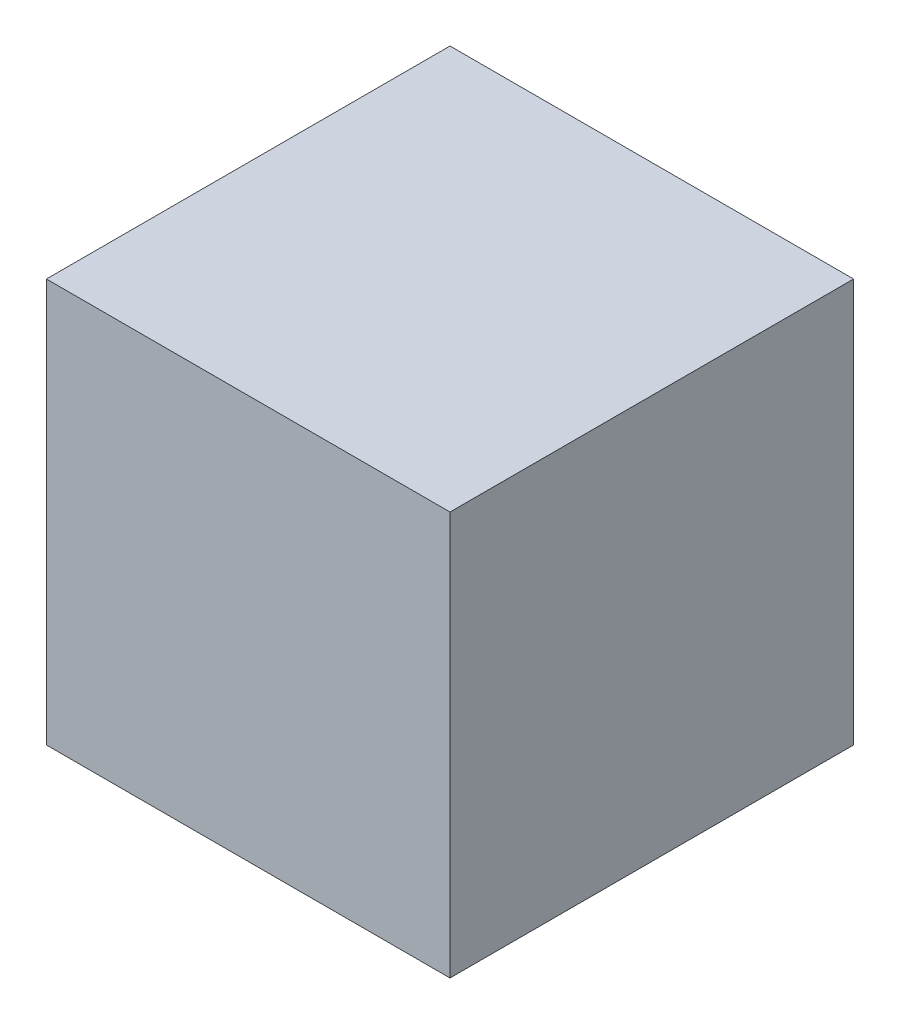
SolidWorks part; units mm, degrees
ref_plane "Ebene vorne" through (0, 0, 0) normal (0, 0, 1) x (1, 0, 0)
ref_plane "Ebene oben" through (0, 0, 0) normal (0, 1, 0) x (1, 0, 0)
ref_plane "Ebene rechts" through (0, 0, 0) normal (1, 0, 0) x (0, 0, -1)
sketch "Skizze1" plane through (0, 0, 0) normal (0, 1, 0) x (1, 0, 0)
  line L1 (-0.5, -0.5) -> (0.5, -0.5)
  line L2 (-0.5, -0.5) -> (-0.5, 0.5)
  line L3 (-0.5, 0.5) -> (0.5, 0.5)
  line L4 (0.5, -0.5) -> (0.5, 0.5)
  line L5 (-0.5, -0.5) -> (0.5, 0.5) construction
  line L6 (-0.5, 0.5) -> (0.5, -0.5) construction
  point P0 (0, 0)
  dimension "D1" = 1
extrude "Aufsatz-Linear austragen1" add sketch "Skizze1" along normal mid plane 1
